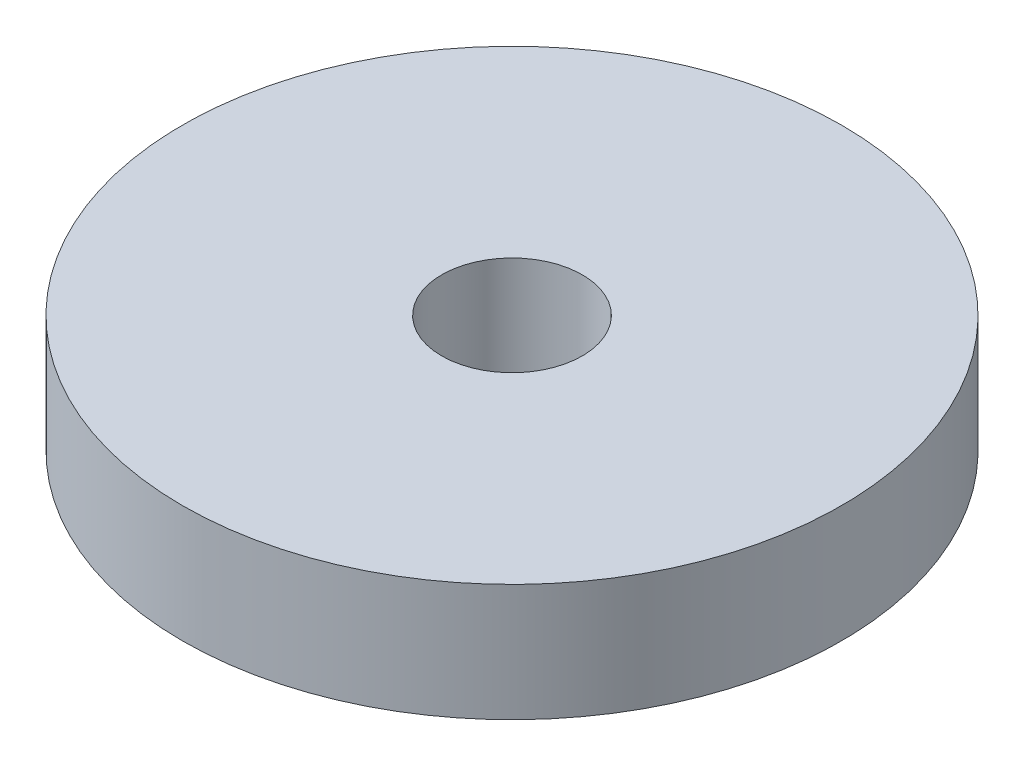
SolidWorks part; units mm, degrees
material "Epoxy, Unfilled"
ref_plane "Front Plane" through (0, 0, 0) normal (0, 0, 1) x (1, 0, 0)
ref_plane "Top Plane" through (0, 0, 0) normal (0, 1, 0) x (1, 0, 0)
ref_plane "Right Plane" through (0, 0, 0) normal (1, 0, 0) x (0, 0, -1)
sketch "Sketch1" plane through (0, 0, 0) normal (0, 1, 0) x (1, 0, 0)
  circle A0 centre (0, 0) radius 8.9294
  dimension "D1" = 17.8587
extrude "Boss-Extrude1" add sketch "Sketch1" along normal blind 3.175 contours A0
sketch "Sketch2" plane through (0, 3.175, 0) normal (0, 1, 0) x (1, 0, 0)
  circle A0 centre (0, 0) radius 1.905
  dimension "D1" = 3.81
extrude "Cut-Extrude1" cut sketch "Sketch2" against normal blind 3.175
